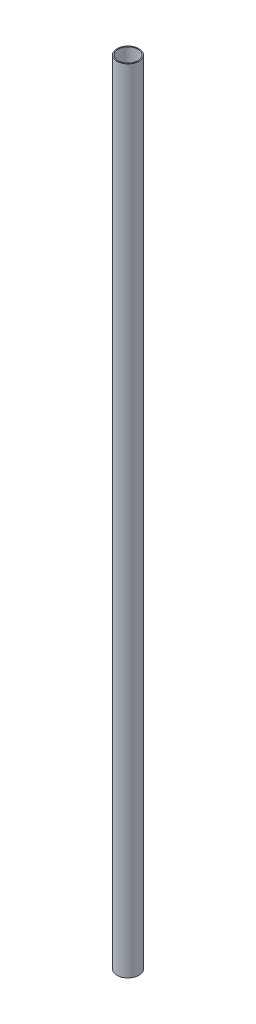
SolidWorks part; units mm, degrees
material "Zoltek Panex 33"
ref_plane "Front Plane" through (0, 0, 0) normal (0, 0, 1) x (1, 0, 0)
ref_plane "Top Plane" through (0, 0, 0) normal (0, 1, 0) x (1, 0, 0)
ref_plane "Right Plane" through (0, 0, 0) normal (1, 0, 0) x (0, 0, -1)
sketch "Sketch1" plane through (0, 0, 0) normal (0, 1, 0) x (1, 0, 0)
  circle A0 centre (0, 0) radius 12.7
  circle A1 centre (0, 0) radius 11.5
  dimension "D1" = 25.4
  dimension "D2" = 23
extrude "Boss-Extrude1" add sketch "Sketch1" along normal blind 915
